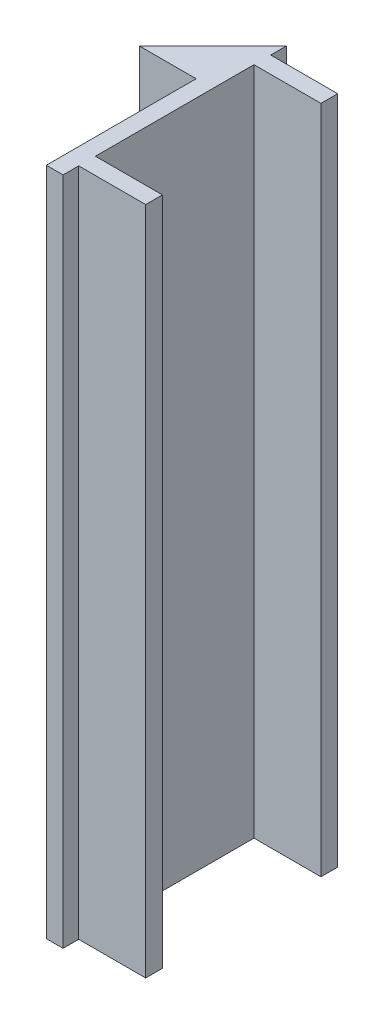
SolidWorks part; units mm, degrees
ref_plane "Front Plane" through (0, 0, 0) normal (0, 0, 1) x (1, 0, 0)
ref_plane "Top Plane" through (0, 0, 0) normal (0, 1, 0) x (1, 0, 0)
ref_plane "Right Plane" through (0, 0, 0) normal (1, 0, 0) x (0, 0, -1)
sketch "Sketch1" plane through (0, 0, 0) normal (0, 1, 0) x (1, 0, 0)
  line L0 (0, 0) -> (25.4, 0)
  line L1 (25.4, 0) -> (25.4, -50.8)
  line L9 (0, 0) -> (32.9, 32.9)
  line L11 (32.9, 32.9) -> (32.9, 25.9)
  line L14 (25.4, -50.8) -> (25.4, -67.1)
  line L15 (25.4, -67.1) -> (32.9, -67.1)
  line L16 (32.9, -67.1) -> (32.9, -60.1)
  line L17 (32.9, 18.4) -> (32.9, -52.6)
  line L18 (32.9, -60.1) -> (62.9, -60.1)
  line L20 (32.9, -52.6) -> (62.9, -52.6)
  line L21 (62.9, -60.1) -> (62.9, -52.6)
  line L22 (32.9, 18.4) -> (62.9, 18.4)
  line L24 (32.9, 25.9) -> (62.9, 25.9)
  line L25 (62.9, 18.4) -> (62.9, 25.9)
  dimension "D1" = 50.8
  dimension "D2" = 25.4
  dimension "D3" = 45
  dimension "D4" = 7
  dimension "D5" = 7.5
  dimension "D6" = 7.5
  dimension "D7" = 30
  dimension "D8" = 7
  dimension "D9" = 71
  dimension "D10" = 100
extrude "Boss-Extrude1" add sketch "Sketch1" along normal blind 300
sketch "Sketch3" plane through (-25.9, 0, -25.9) normal (0, 0, 1) x (1, 0, 0)
  line L0 (58.8, 300) -> (25.9, 300) construction
  line L1 (38.6, 25) -> (38.6, 275) construction
  line L2 (25.9, 300) -> (25.9, 0) construction
  circle A0 centre (38.6, 275) radius 2.5
  circle A1 centre (38.6, 200) radius 2.5
  circle A2 centre (38.6, 100) radius 2.5
  circle A3 centre (38.6, 25) radius 2.5
  dimension "D5" = 5
  dimension "D6" = 5
  dimension "D7" = 5
  dimension "D8" = 5
  dimension "D1" = 25
  dimension "D2" = 75
  dimension "D3" = 100
  dimension "D4" = 75
  dimension "D9" = 12.7
extrude "Cut-Extrude1" cut sketch "Sketch3" along normal blind 51
sketch "Sketch4" plane through (0, 0, -25.9) normal (0, 0, -1) x (-1, 0, 0)
  circle A0 centre (-12.7, 275) radius 5
  circle A1 centre (-12.7, 200) radius 5
  circle A2 centre (-12.7, 100) radius 5
  circle A3 centre (-12.7, 25) radius 5
  dimension "D1" = 10
  dimension "D2" = 10
  dimension "D3" = 10
  dimension "D4" = 10
extrude "Cut-Extrude2" cut sketch "Sketch4" against normal blind 19
